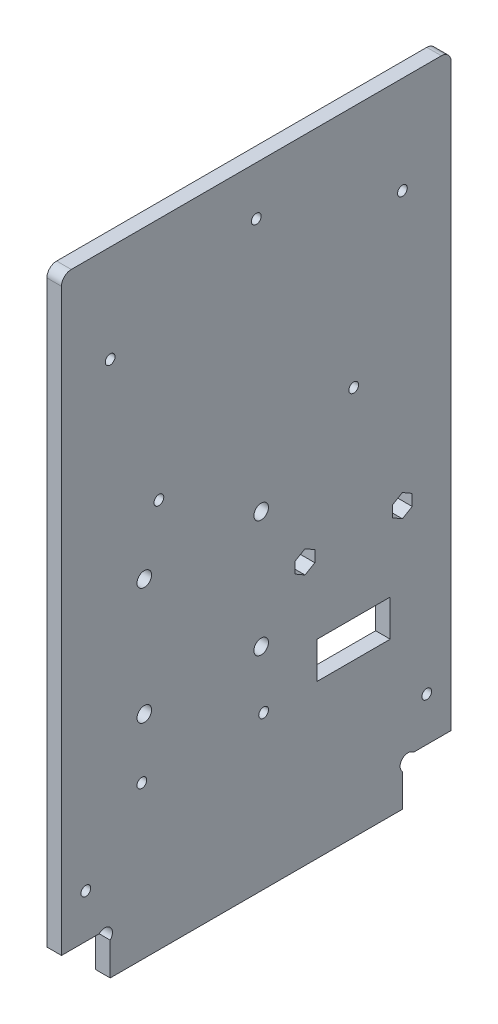
SolidWorks part; units mm, degrees
ref_plane "Plan de face" through (0, 0, 0) normal (0, 0, 1) x (1, 0, 0)
ref_plane "Plan de dessus" through (0, 0, 0) normal (0, 1, 0) x (1, 0, 0)
ref_plane "Plan de droite" through (0, 0, 0) normal (1, 0, 0) x (0, 0, -1)
sketch "Esquisse1" plane through (0, 0, 0) normal (1, 0, 0) x (0, 0, -1)
  line L8 (10, 6.7373) -> (10, 0)
  line L9 (70, 6.7373) -> (70, 0)
  line L10 (7.7373, 9) -> (0, 9)
  line L11 (10, 0) -> (70, 0)
  line L12 (72.2627, 9) -> (80, 9)
  line L13 (0, 9) -> (0, 130)
  line L14 (0, 130) -> (80, 130)
  line L15 (80, 130) -> (80, 9)
  arc A0 (10, 6.7373) -> (7.7373, 9) centre (8.8686, 7.8686) ccw
  arc A1 (70, 6.7373) -> (72.2627, 9) centre (71.1314, 7.8686) cw
  dimension "D7" = 1.1314
  dimension "D6" = 1.6
  dimension "D1" = 9
  dimension "D2" = 10
  dimension "D3" = 10
  dimension "D4" = 80
  dimension "D5" = 130
  dimension "D8" = 1.1314
  dimension "D9" = 1.1314
  dimension "D10" = 1.1314
extrude "Extrusion1" add sketch "Esquisse1" along normal blind 3
sketch "Esquisse2" plane through (3, 0, 0) normal (1, 0, 0) x (0, 0, -1)
  line L0 (0, 9) -> (7.7373, 9) construction
  line L1 (0, 130) -> (0, 9) construction
  line L2 (80, 9) -> (80, 130) construction
  line L3 (72.2627, 9) -> (80, 9) construction
  line L4 (80, 130) -> (0, 130) construction
  circle A0 centre (60, 80) radius 1
  circle A1 centre (10, 110) radius 1
  circle A2 centre (20, 80) radius 1
  circle A3 centre (70, 110) radius 1
  circle A4 centre (17, 67.45) radius 1.5
  circle A5 centre (17, 43.45) radius 1.5
  circle A6 centre (41, 43.45) radius 1.5
  circle A7 centre (41, 67.45) radius 1.5
  circle A8 centre (40, 120) radius 1
  circle A9 centre (70, 54) radius 1
  circle A10 centre (50, 54) radius 1
  dimension "D5" = 17
  dimension "D7" = 10
  dimension "D9" = 10
  dimension "D4" = 3
  dimension "D6" = 2
  dimension "D1" = 58.45
  dimension "D2" = 24
  dimension "D3" = 24
  dimension "D8" = 40
  dimension "D10" = 30
  dimension "D11" = 10
  dimension "D12" = 20
  dimension "D13" = 10
  dimension "D14" = 10
  dimension "D15" = 10
  dimension "D16" = 20
  dimension "D17" = 45
extrude "Enlèv. mat.-Extru.1" cut sketch "Esquisse2" against normal through all
sketch "Esquisse3" plane through (0, 0, 0) normal (-1, 0, 0) x (0, 0, 1)
  line L1 (-67.5, 39) -> (-52.5, 39)
  line L2 (-67.5, 39) -> (-67.5, 31.5)
  line L3 (-67.5, 31.5) -> (-52.5, 31.5)
  line L4 (-52.5, 39) -> (-52.5, 31.5)
  circle A0 centre (-70, 54) radius 1 construction
  circle A1 centre (-50, 54) radius 1 construction
  dimension "D4" = 2.5
  dimension "D1" = 15
  dimension "D2" = 7.5
  dimension "D3" = 15
  dimension "D5" = 2.5
extrude "Enlèv. mat.-Extru.2" cut sketch "Esquisse3" against normal through all
sketch "Esquisse4" plane through (3, 0, 0) normal (1, 0, 0) x (0, 0, -1)
  line L3 (0, 9) -> (7.7373, 9) construction
  line L4 (0, 130) -> (0, 9) construction
  line L5 (80, 9) -> (80, 130) construction
  circle A2 centre (75, 18) radius 1
  circle A3 centre (5, 18) radius 1
  dimension "D1" = 2
  dimension "D2" = 5
  dimension "D3" = 5
  dimension "D5" = 9
extrude "Enlèv. mat.-Extru.3" cut sketch "Esquisse4" against normal through all
sketch "Esquisse5" plane through (3, 0, 0) normal (1, 0, 0) x (0, 0, -1)
  line L0 (80, 9) -> (80, 130) construction
  line L1 (50, 51.67) -> (52.0178, 52.835)
  line L2 (52.0178, 52.835) -> (52.0178, 55.165)
  line L3 (52.0178, 55.165) -> (50, 56.33)
  line L4 (50, 56.33) -> (47.9822, 55.165)
  line L5 (47.9822, 55.165) -> (47.9822, 52.835)
  line L6 (47.9822, 52.835) -> (50, 51.67)
  line L7 (70, 51.67) -> (72.0178, 52.835)
  line L8 (72.0178, 52.835) -> (72.0178, 55.165)
  line L9 (72.0178, 55.165) -> (70, 56.33)
  line L10 (70, 56.33) -> (67.9822, 55.165)
  line L11 (67.9822, 55.165) -> (67.9822, 52.835)
  line L12 (67.9822, 52.835) -> (70, 51.67)
  circle A0 centre (50, 54) radius 2.0178 construction
  circle A1 centre (70, 54) radius 2.0178 construction
  dimension "D1" = 2.33
  dimension "D2" = 2.33
extrude "Enlèv. mat.-Extru.4" cut sketch "Esquisse5" against normal through all
fillet "Congé1" radius 2 2 edges at (1.5, 130, -80) (1.5, 130, 0)
sketch "Esquisse6" plane through (3, 0, 0) normal (1, 0, 0) x (0, 0, -1)
  line L0 (17, 43.45) -> (17, 35.9367) construction
  line L1 (41, 43.45) -> (41, 36.8364) construction
  circle A0 centre (16.5, 31.4604) radius 1
  circle A1 centre (41.5, 31.45) radius 1
  point P4 (0, 0)
  point P5 (0, 0)
  dimension "D1" = 2
  dimension "D4" = 24
  dimension "D2" = 25
  dimension "D3" = 12
  dimension "D5" = 0.5
extrude "Enlèv. mat.-Extru.5" cut sketch "Esquisse6" against normal through all
